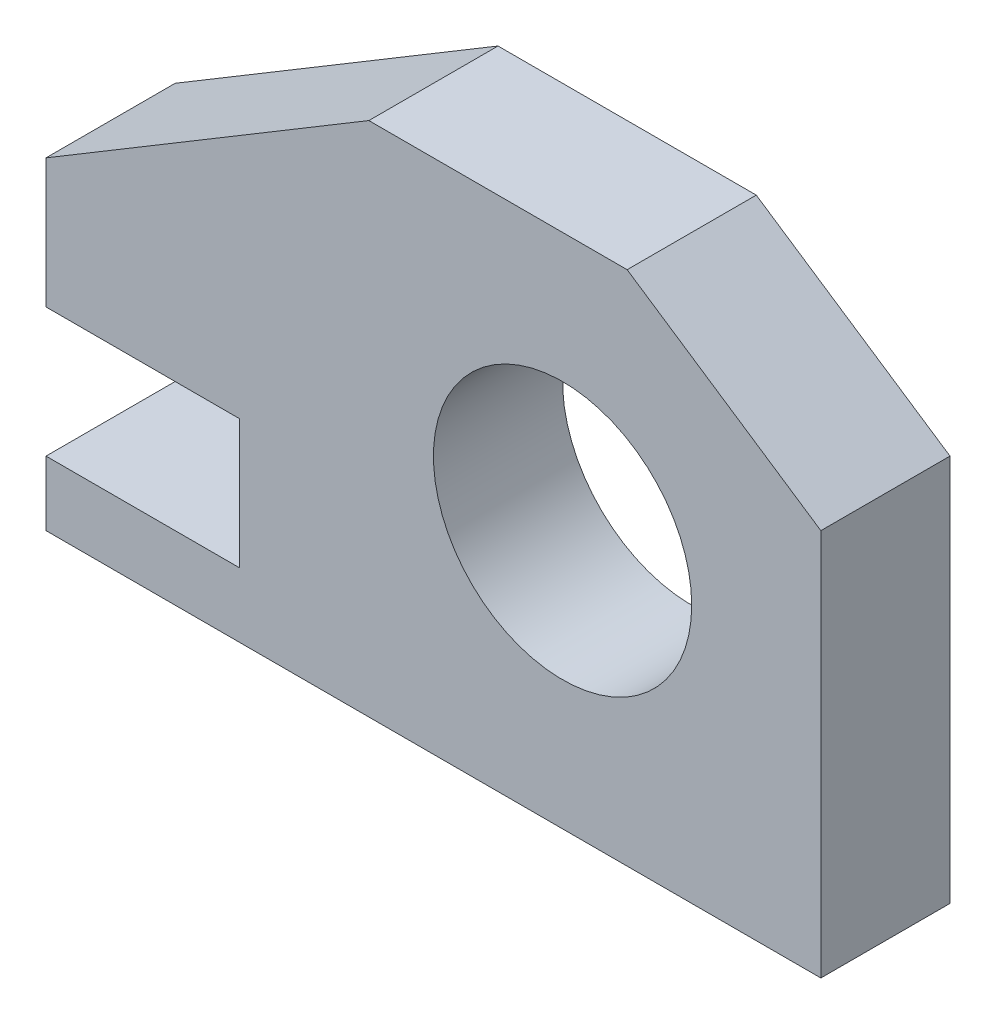
SolidWorks part; units mm, degrees
ref_plane "Front Plane" through (0, 0, 0) normal (0, 0, 1) x (1, 0, 0)
ref_plane "Top Plane" through (0, 0, 0) normal (0, 1, 0) x (1, 0, 0)
ref_plane "Right Plane" through (0, 0, 0) normal (1, 0, 0) x (0, 0, -1)
sketch "Sketch1" plane through (0, 0, 0) normal (0, 0, 1) x (1, 0, 0)
  line L0 (0, 0) -> (0, 38.1)
  line L1 (0, 38.1) -> (-19.05, 50.8)
  line L2 (-19.05, 50.8) -> (-44.45, 50.8)
  line L3 (-44.45, 50.8) -> (-76.2, 31.75)
  line L4 (-76.2, 31.75) -> (-76.2, 19.05)
  line L5 (-76.2, 19.05) -> (-57.15, 19.05)
  line L6 (-57.15, 19.05) -> (-57.15, 6.35)
  line L7 (-57.15, 6.35) -> (-76.2, 6.35)
  line L8 (-76.2, 6.35) -> (-76.2, 0)
  line L9 (-76.2, 0) -> (0, 0)
  circle A0 centre (-25.4, 25.4) radius 12.7
  dimension "D9" = 25.4
  dimension "D1" = 50.8
  dimension "D2" = 31.75
  dimension "D3" = 6.35
  dimension "D4" = 12.7
  dimension "D5" = 19.05
  dimension "D6" = 76.2
  dimension "D7" = 19.05
  dimension "D8" = 25.4
  dimension "D10" = 25.4
  dimension "D11" = 25.4
  dimension "D12" = 38.1
  dimension "D13" = 12.7
extrude "Boss-Extrude1" add sketch "Sketch1" along normal blind 12.7
